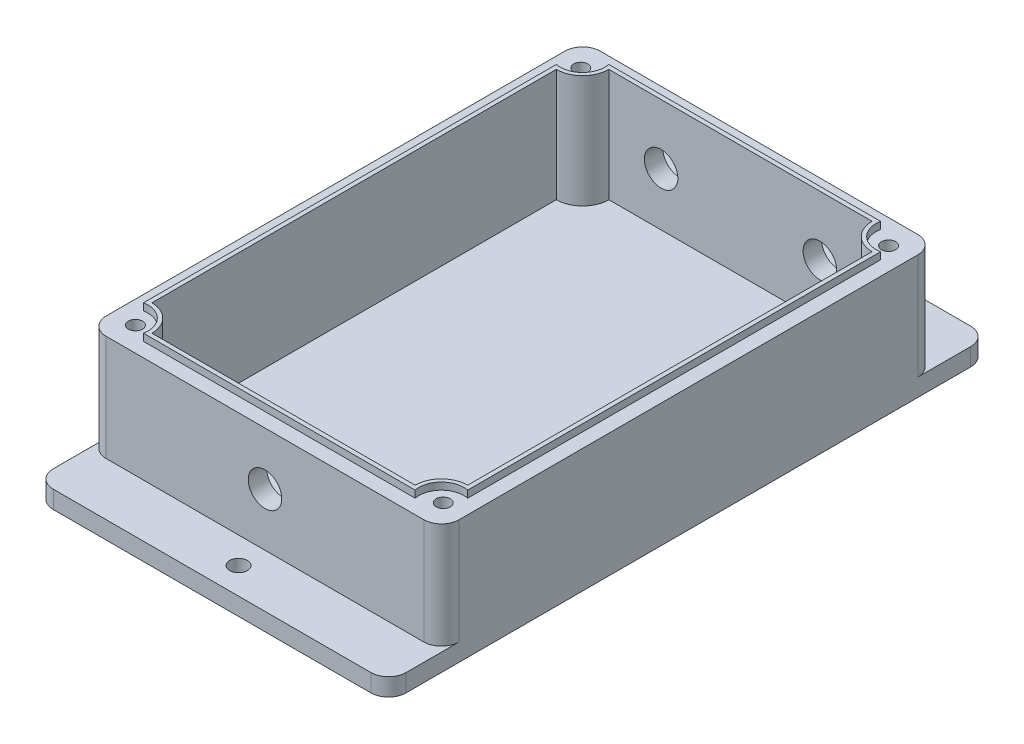
SolidWorks part; units mm, degrees
ref_plane "Front Plane" through (0, 0, 0) normal (0, 0, 1) x (1, 0, 0)
ref_plane "Top Plane" through (0, 0, 0) normal (0, 1, 0) x (1, 0, 0)
ref_plane "Right Plane" through (0, 0, 0) normal (1, 0, 0) x (0, 0, -1)
sketch "Wall" plane through (0, 0, 0) normal (0, 1, 0) x (1, 0, 0)
  line L0 (0, -70) -> (0, 70) construction
  line L1 (-50, 0) -> (50, 0) construction
  line L2 (-50, -70) -> (-50, 70)
  line L3 (-50, 70) -> (50, 70)
  line L4 (50, 70) -> (50, -70)
  line L5 (50, -70) -> (-50, -70)
  line L6 (0, 70) -> (0, 64.75) construction
  line L7 (-50, 0) -> (-44.75, 0) construction
  line L8 (-44.75, -64.75) -> (-44.75, 64.75)
  line L9 (44.75, 64.75) -> (-44.75, 64.75)
  line L10 (44.75, 64.75) -> (44.75, -64.75)
  line L11 (-44.75, -64.75) -> (44.75, -64.75)
  arc A0 (-37.3, 64.75) -> (-44.75, 57.3) centre (-44.75, 64.75) cw
  arc A1 (37.3, 64.75) -> (44.75, 57.3) centre (44.75, 64.75) ccw
  arc A2 (-44.75, -57.3) -> (-37.3, -64.75) centre (-44.75, -64.75) cw
  arc A3 (37.3, -64.75) -> (44.75, -57.3) centre (44.75, -64.75) cw
  point P4 (0, 0)
  point P8 (0, 0)
  point P10 (-50, 0)
  point P17 (-44.75, 0)
  point P20 (0, 64.75)
  dimension "D5" = 7.45
  dimension "D1" = 140
  dimension "D2" = 100
  dimension "D3" = 5.25
  dimension "D4" = 5.25
sketch "Base" plane through (0, 0, 0) normal (0, 1, 0) x (1, 0, 0)
  line L0 (-50, -70) -> (-50, 70)
  line L1 (50, -70) -> (50, 70)
  line L2 (-50, 70) -> (-50, 85)
  line L4 (50, 70) -> (50, 85)
  line L5 (50, 85) -> (-50, 85)
  line L6 (-50, -70) -> (-50, -85)
  line L7 (-50, -85) -> (50, -85)
  line L8 (50, -85) -> (50, -70)
  point P4 (-50, 0)
  point P10 (50, 0)
  dimension "D1" = 15
extrude "Bottom" add sketch "Base" against normal blind 5
extrude "Walls" add sketch "Wall" along normal blind 30 contours L5 L4 L3 L2 L11 L8 L9 L10 | A2 L8 L11 | A3 L11 L10 | A0 L9 L8 | L9 A1 L10
ref_plane "Drill" through (0, 30, 0) normal (0, -1, 0) x (-1, 0, 0)
fillet "MainFillet" radius 5 8 edges at (-50, -2.5, -85) (50, -2.5, -85) (50, -2.5, 85) (-50, -2.5, 85) (-50, 15, -70) (50, 15, -70) (-50, 15, 70) (50, 15, 70)
sketch "DrillHoles" plane through (0, 30, 0) normal (0, -1, 0) x (-1, 0, 0)
  line L0 (0, -64.75) -> (0, 64.75) construction
  line L1 (-37.3, 64.75) -> (37.3, 64.75) construction
  line L2 (-44.75, -64.75) -> (44.75, 64.75) construction
  line L3 (44.75, -64.75) -> (-44.75, 64.75) construction
  line L4 (44.75, 64.75) -> (43.6129, 63.1047) construction
  line L5 (-44.75, 64.75) -> (-43.6129, 63.1047) construction
  line L6 (-44.75, -64.75) -> (-43.6129, -63.1047) construction
  line L7 (44.75, -64.75) -> (43.6129, -63.1047) construction
  circle A0 centre (43.6129, 63.1047) radius 2
  circle A1 centre (43.6129, -63.1047) radius 2
  circle A2 centre (-43.6129, -63.1047) radius 2
  circle A3 centre (-43.6129, 63.1047) radius 2
  point P6 (0, 0)
  point P10 (0, 0)
  point P14 (0, 0)
  dimension "D1" = 2
  dimension "D2" = 2
  dimension "D3" = 2
  dimension "D4" = 2
extrude "Drilling" cut sketch "DrillHoles" along normal blind 45
sketch "GasketInsert" plane through (0, 30, 0) normal (0, 1, 0) x (1, 0, 0)
  line L0 (0, -64.75) -> (0, 64.75) construction
  line L1 (37.3, 64.75) -> (-37.3, 64.75) construction
  line L2 (-44.75, 0) -> (44.75, 0) construction
  line L3 (44.75, 57.3) -> (44.75, -57.3) construction
  line L4 (-44.75, -64.75) -> (44.75, 64.75) construction
  line L5 (44.75, -64.75) -> (-44.75, 64.75) construction
  line L6 (-44.75, 0) -> (-45.95, 0) construction
  line L7 (-45.95, -58.5) -> (-45.95, 58.5)
  line L10 (0, 64.75) -> (0, 65.95) construction
  line L11 (-38.5, 65.95) -> (38.5, 65.95)
  line L12 (44.75, 0) -> (45.95, 0) construction
  line L13 (45.95, -58.5) -> (45.95, 58.5)
  line L18 (0, -64.75) -> (0, -65.95) construction
  line L19 (-38.5, -65.95) -> (38.5, -65.95)
  line L23 (-37.3, -64.75) -> (37.3, -64.75)
  line L26 (-37.3, -64.75) -> (37.3, -64.75) construction
  line L27 (44.75, -57.3) -> (44.75, 57.3)
  line L28 (-37.3, 64.75) -> (37.3, 64.75)
  line L29 (-44.75, -57.3) -> (-44.75, 57.3)
  arc A4 (-37.3, 64.75) -> (-44.75, 57.3) centre (-44.75, 64.75) cw
  arc A5 (37.3, 64.75) -> (44.75, 57.3) centre (44.75, 64.75) ccw
  arc A6 (37.3, 64.75) -> (44.75, 57.3) centre (44.75, 64.75) ccw construction
  arc A7 (44.75, -57.3) -> (37.3, -64.75) centre (44.75, -64.75) ccw
  arc A8 (44.75, -57.3) -> (37.3, -64.75) centre (44.75, -64.75) ccw construction
  arc A9 (-44.75, -57.3) -> (-37.3, -64.75) centre (-44.75, -64.75) cw
  arc A10 (-37.3, -64.75) -> (-44.75, -57.3) centre (-44.75, -64.75) ccw construction
  arc A11 (38.5, -65.95) -> (45.95, -58.5) centre (44.75, -64.75) cw
  arc A12 (-38.5, -65.95) -> (-45.95, -58.5) centre (-44.75, -64.75) ccw
  arc A13 (-38.5, 65.95) -> (-45.95, 58.5) centre (-44.75, 64.75) cw
  arc A14 (38.5, 65.95) -> (45.95, 58.5) centre (44.75, 64.75) ccw
  point P6 (0, 0)
  point P12 (0, 0)
  point P14 (0, 0)
  point P17 (0, 0)
  point P18 (0, 0)
  point P23 (-45.95, 0)
  point P24 (0, 0)
  point P35 (0, 65.95)
  point P38 (38.5, 65.95)
  point P39 (45.95, 0)
  point P43 (45.95, 58.5)
  point P45 (0, -65.95)
  point P48 (38.5, -65.95)
  point P52 (0, -64.75)
  point P55 (44.75, 0)
  point P57 (44.75, 0)
  point P58 (0, -64.75)
  point P63 (0, 64.75)
  point P68 (-44.75, 0)
  dimension "D1" = 1.2
  dimension "D6" = 1.2
  dimension "D2" = 1.2
  dimension "D3" = 1.2
  dimension "D7" = 1.2
extrude "Gasket" add sketch "GasketInsert" along normal blind 2
sketch "IO Holes" plane through (0, 0, 0) normal (0, 0, 1) x (1, 0, 0)
  line L0 (0, 0) -> (0, 30) construction
  line L1 (-38.5, 30) -> (38.5, 30) construction
  line L2 (0, 15) -> (-45, 15) construction
  line L3 (-45, 30) -> (-45, 0) construction
  line L4 (0, 15) -> (45, 15) construction
  line L5 (45, 0) -> (45, 30) construction
  circle A0 centre (-22.5, 15) radius 4.75
  circle A1 centre (22.5, 15) radius 4.75
  dimension "D1" = 9.5
  dimension "D2" = 9.5
sketch "Sketch1" plane through (0, 0, 70) normal (0, 0, 1) x (1, 0, 0)
  line L0 (0, 0) -> (0, 30) construction
  line L1 (-38.5, 30) -> (38.5, 30) construction
  circle A0 centre (0, 15) radius 4.75
  dimension "D1" = 9.5
extrude "Cut-Extrude1" cut sketch "Sketch1" against normal blind 10
extrude "Cut-Extrude2" cut sketch "IO Holes" against normal up to surface (70 mm away) up to face at (0, 15, -70)
sketch "Sketch2" plane through (0, 0, 0) normal (0, 1, 0) x (1, 0, 0)
  line L0 (0, 85) -> (0, 70) construction
  line L1 (45, 85) -> (-45, 85) construction
  line L2 (-45, 70) -> (45, 70) construction
  line L3 (0, -70) -> (0, -85) construction
  line L4 (45, -70) -> (-45, -70) construction
  line L5 (-45, -85) -> (45, -85) construction
  circle A0 centre (0, 77.5) radius 2.5
  circle A1 centre (0, -77.5) radius 2.5
  dimension "D1" = 5
  dimension "D2" = 5
extrude "Cut-Extrude3" cut sketch "Sketch2" against normal blind 10
